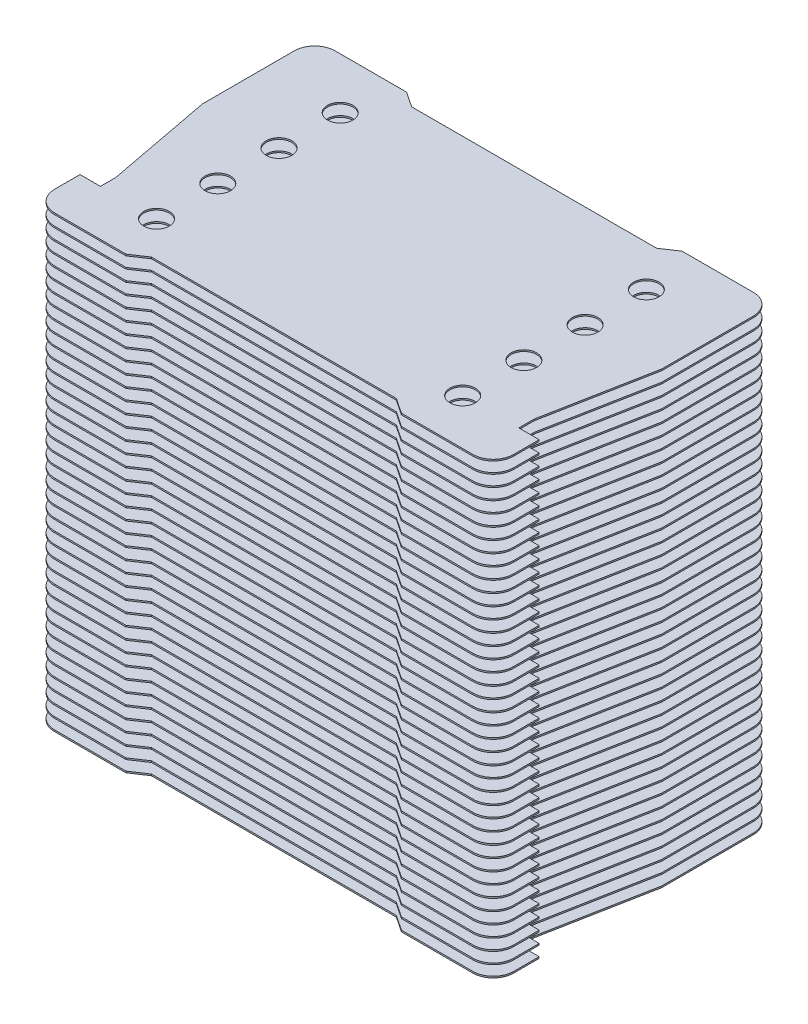
SolidWorks part; units mm, degrees
ref_plane "Front Plane" through (0, 0, 0) normal (0, 0, 1) x (1, 0, 0)
ref_plane "Top Plane" through (0, 0, 0) normal (0, 1, 0) x (1, 0, 0)
ref_plane "Right Plane" through (0, 0, 0) normal (1, 0, 0) x (0, 0, -1)
sketch "Sketch1" plane through (0, 0, 0) normal (0, 1, 0) x (1, 0, 0)
  line L0 (27, 27.5) -> (41, 27.5)
  line L1 (-41, -27.5) -> (-27, -27.5)
  line L2 (-45, -23.5) -> (-45, -17.8054)
  line L3 (-41, 27.5) -> (-27, 27.5)
  line L4 (45, -23.5) -> (45, -17.8054)
  line L5 (-45, -27.5) -> (45, 27.5) construction
  line L6 (-45, 27.5) -> (45, -27.5) construction
  line L7 (-24, 25.5) -> (24, 25.5)
  line L8 (-45, 5.5) -> (-45, 23.5)
  line L9 (24, 25.5) -> (27, 27.5)
  line L10 (27, -27.5) -> (41, -27.5)
  line L11 (-24, 25.5) -> (-27, 27.5)
  line L12 (24, -25.5) -> (27, -27.5)
  line L13 (-24, -25.5) -> (-27, -27.5)
  line L14 (-24, -25.5) -> (24, -25.5)
  line L15 (45, 5.5) -> (45, 23.5)
  line L16 (43.7396, -16.8399) -> (41, -17.5786)
  line L17 (-43.7396, -16.8399) -> (-41, -17.5786)
  line L18 (-41, -17.5786) -> (-45, 5.5)
  line L19 (41, -17.5786) -> (45, 5.5)
  arc A0 (41, -27.5) -> (45, -23.5) centre (41, -23.5) ccw
  arc A1 (-41, -27.5) -> (-45, -23.5) centre (-41, -23.5) cw
  arc A2 (45, 23.5) -> (41, 27.5) centre (41, 23.5) ccw
  arc A3 (-45, 23.5) -> (-41, 27.5) centre (-41, 23.5) cw
  circle A4 centre (-30, 17.5) radius 2.5
  circle A5 centre (-30, 5.5) radius 2.5
  circle A6 centre (-30, -6.5) radius 2.5
  circle A7 centre (-30, -18.5) radius 2.5
  circle A8 centre (30, -18.5) radius 2.5
  circle A9 centre (30, -6.5) radius 2.5
  circle A10 centre (30, 5.5) radius 2.5
  circle A11 centre (30, 17.5) radius 2.5
  arc A12 (-45, -17.8054) -> (-43.7396, -16.8399) centre (-44, -17.8054) cw
  arc A13 (45, -17.8054) -> (43.7396, -16.8399) centre (44, -17.8054) ccw
  point P0 (0, 0)
  dimension "D2" = 4
  dimension "D3" = 10
  dimension "D5" = 1
  dimension "D1" = 55
  dimension "D4" = 4
extrude "Boss-Extrude1" add sketch "Sketch1" along normal blind 0.3
sketch "Sketch2" plane through (0, 0, 0) normal (0, 0, 1) x (1, 0, 0)
  line L0 (0, 0) -> (0, 90) construction
pattern_linear "LPattern2" count 40 spacing 2.25 along (0, 1, 0) of "Boss-Extrude1"
ref_plane "Plane1" through (0, 0, 0) normal (0, -1, 0) x (-1, 0, 0)
ref_plane "Plane2" through (0, 0, 0) normal (1, 0, 0) x (0, 0, -1)
ref_plane "Plane3" through (0, 44.025, 0) normal (0, -1, 0) x (-1, 0, 0)
sketch "Sketch3" plane through (0, 0, 0) normal (0, -1, 0) x (1, 0, 0)
  line L1 (41, 18.5) -> (45, 18.5)
  line L2 (45, 23.5) -> (45, 17.8054) construction
  line L3 (41, 18.5) -> (41, 15.5)
  line L4 (41, 15.5) -> (45, -5.5)
  line L5 (45, -5.5) -> (47.216, -5.5)
  line L6 (47.216, -5.5) -> (47.216, 18.5)
  line L7 (47.216, 18.5) -> (45, 18.5)
  line L9 (-47.216, 18.5) -> (-45, 18.5)
  line L10 (-47.216, -5.5) -> (-47.216, 18.5)
  line L11 (-45, -5.5) -> (-47.216, -5.5)
  line L12 (-41, 15.5) -> (-45, -5.5)
  line L13 (-41, 18.5) -> (-41, 15.5)
  line L14 (-41, 18.5) -> (-45, 18.5)
extrude "Cut-Extrude1" cut sketch "Sketch3" against normal up to surface (88.05 mm away) up to face at (30, 88.05, -8)
